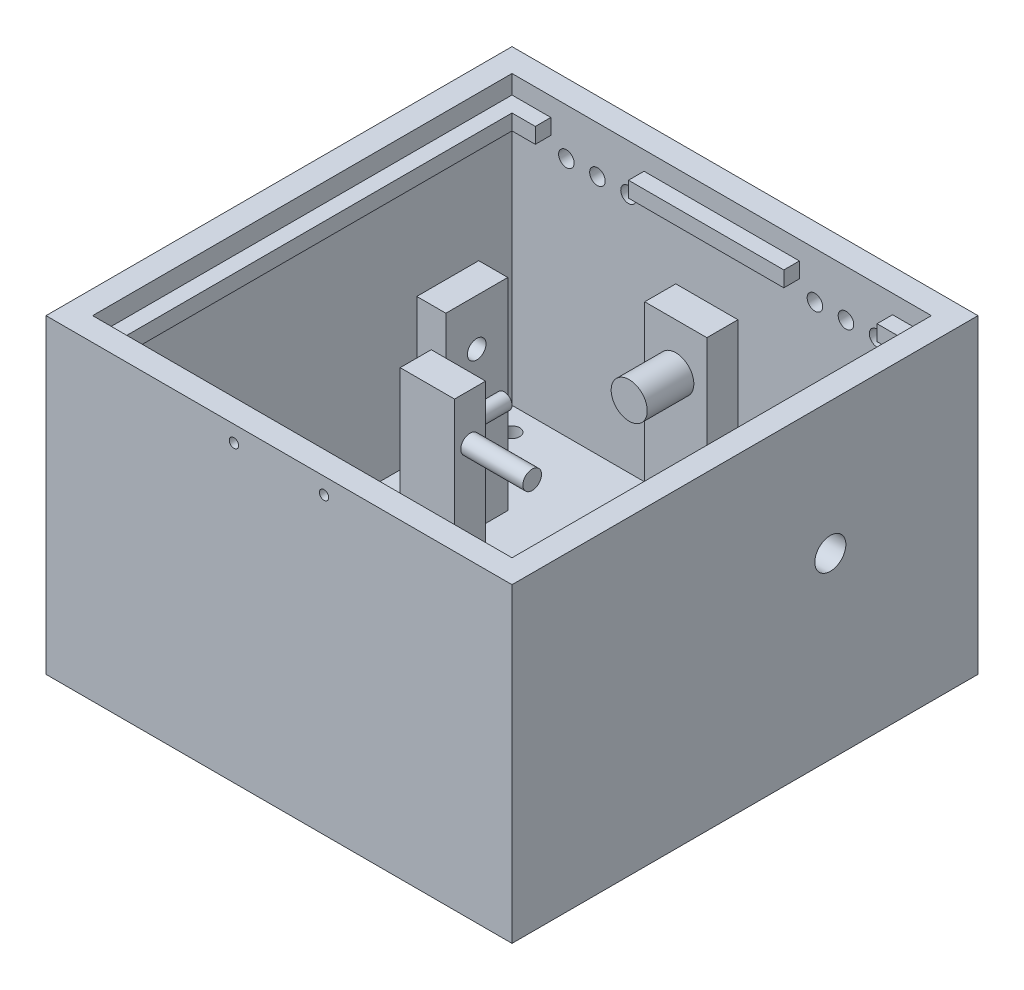
SolidWorks part; units mm, degrees
material "Cedar"
ref_plane "Front" through (0, 0, 0) normal (0, 0, 1) x (1, 0, 0)
ref_plane "Top" through (0, 0, 0) normal (0, 1, 0) x (1, 0, 0)
ref_plane "Right" through (0, 0, 0) normal (1, 0, 0) x (0, 0, -1)
sketch "Sketch1" plane through (0, 0, 0) normal (0, 1, 0) x (1, 0, 0)
  line L1 (-75, -75) -> (75, -75)
  line L2 (-75, -75) -> (-75, 75)
  line L3 (-75, 75) -> (75, 75)
  line L4 (75, -75) -> (75, 75)
  line L5 (-75, -75) -> (75, 75) construction
  line L6 (-75, 75) -> (75, -75) construction
  point P0 (0, 0)
  dimension "D1" = 150
  dimension "D2" = 150
extrude "Boss-Extrude1" add sketch "Sketch1" along normal blind 7.5
sketch "Sketch2" plane through (0, 7.5, 0) normal (0, 1, 0) x (1, 0, 0)
  line L1 (-67.5, -67.5) -> (67.5, -67.5)
  line L2 (-67.5, -67.5) -> (-67.5, 67.5)
  line L3 (-67.5, 67.5) -> (67.5, 67.5)
  line L4 (67.5, -67.5) -> (67.5, 67.5)
  line L5 (-67.5, -67.5) -> (67.5, 67.5) construction
  line L6 (-67.5, 67.5) -> (67.5, -67.5) construction
  line L7 (-75, -75) -> (75, -75)
  line L8 (-75, -75) -> (-75, 75)
  line L9 (-75, 75) -> (75, 75)
  line L10 (75, -75) -> (75, 75)
  line L11 (-75, -75) -> (75, 75) construction
  line L12 (-75, 75) -> (75, -75) construction
  point P0 (0, 0)
  point P5 (0, 0)
  dimension "D1" = 135
  dimension "D2" = 135
extrude "Boss-Extrude2" add sketch "Sketch2" along normal blind 92.5
sketch "Sketch3" plane through (0, 7.5, 0) normal (0, 1, 0) x (1, 0, 0)
  line L0 (0, -4.125) -> (0, 4.125) construction
  line L1 (-10, 62.7245) -> (10, 62.7245)
  line L2 (-10, 62.7245) -> (-10, 52.7245)
  line L3 (-10, 52.7245) -> (10, 52.7245)
  line L4 (10, 62.7245) -> (10, 52.7245)
  line L5 (-10, 62.7245) -> (10, 52.7245) construction
  line L6 (-10, 52.7245) -> (10, 62.7245) construction
  point P0 (0, 57.7245)
  dimension "D1" = 10
  dimension "D2" = 20
extrude "Boss-Extrude3" add sketch "Sketch3" along normal blind 65
sketch "Sketch4" plane through (0, 0, -52.7245) normal (0, 0, 1) x (1, 0, 0)
  line L0 (0, -4.125) -> (0, 4.125) construction
  line L2 (-10, 7.5) -> (10, 7.5) construction
  circle A0 centre (0, 57.5) radius 5.8075
  dimension "D1" = 11.615
  dimension "D2" = 50
extrude "Boss-Extrude4" add sketch "Sketch4" along normal blind 15 contours A0
sketch "Sketch5" plane through (0, 7.5, 0) normal (0, 1, 0) x (1, 0, 0)
  line L0 (-67.5, -67.5) -> (67.5, -67.5) construction
  line L1 (-48.1782, 37.4665) -> (-38.8218, 37.4665)
  line L2 (-48.1782, 37.4665) -> (-48.1782, 17.5335)
  line L3 (-48.1782, 17.5335) -> (-38.8218, 17.5335)
  line L4 (-38.8218, 37.4665) -> (-38.8218, 17.5335)
  line L5 (-48.1782, 37.4665) -> (-38.8218, 17.5335) construction
  line L6 (-48.1782, 17.5335) -> (-38.8218, 37.4665) construction
  line L7 (-67.5, 67.5) -> (-67.5, -67.5) construction
  point P0 (-43.5, 27.5)
  dimension "D1" = 95
  dimension "D2" = 9.3563
  dimension "D3" = 19.933
  dimension "D4" = 24
extrude "Boss-Extrude5" add sketch "Sketch5" along normal blind 65
sketch "Sketch6" plane through (-38.8218, 0, 0) normal (1, 0, 0) x (0, 0, -1)
  line L1 (17.5335, 7.5) -> (37.4665, 7.5) construction
  line L2 (37.4665, 72.5) -> (37.4665, 7.5) construction
  circle A0 centre (27.4665, 57.5) radius 3
  dimension "D1" = 6
  dimension "D2" = 50
  dimension "D3" = 10
sketch "Sketch7" plane through (0, 7.5, 0) normal (0, 1, 0) x (1, 0, 0)
  line L0 (-67.5, -67.5) -> (67.5, -67.5) construction
  line L1 (-23.5, 0) -> (-13.5, 0)
  line L2 (-23.5, 0) -> (-23.5, -5)
  line L3 (-23.5, -5) -> (-13.5, -5)
  line L4 (-13.5, 0) -> (-13.5, -5)
  line L5 (-23.5, 0) -> (-13.5, -5) construction
  line L6 (-23.5, -5) -> (-13.5, 0) construction
  line L7 (-67.5, 67.5) -> (-67.5, -67.5) construction
  line L9 (-23.5, 0) -> (-31, 0)
  line L10 (-23.5, 0) -> (-23.5, -5)
  line L11 (-23.5, -5) -> (-31, -5)
  line L12 (-31, 0) -> (-31, -5)
  point P0 (-18.5, -2.5)
  dimension "D1" = 5
  dimension "D2" = 10
  dimension "D3" = 65
  dimension "D4" = 49
  dimension "D5" = 7.5
  dimension "D6" = 5
extrude "Boss-Extrude7" add sketch "Sketch7" along normal blind 65 contours L9 L12 L11 L2 | L4 L1 L2 L3
sketch "Sketch8" plane through (0, 0, 0) normal (0, 0, -1) x (-1, 0, 0)
  line L0 (13.5, 7.5) -> (31, 7.5) construction
  line L1 (13.5, 72.5) -> (13.5, 7.5) construction
  circle A0 centre (20, 57.5) radius 2.5
  dimension "D1" = 5
  dimension "D2" = 50
  dimension "D3" = 6.5
extrude "Boss-Extrude8" add sketch "Sketch8" along normal blind 17.5
sketch "Sketch9" plane through (-13.5, 0, 0) normal (1, 0, 0) x (0, 0, -1)
  line L0 (-5, 72.5) -> (-5, 7.5) construction
  line L1 (-5, 7.5) -> (0, 7.5) construction
  circle A0 centre (10, 57.5) radius 3
  dimension "D1" = 6
  dimension "D2" = 15
  dimension "D3" = 50
sketch "Sketch10" plane through (0, 7.5, 0) normal (0, 1, 0) x (1, 0, 0)
  line L1 (-31, 0) -> (-13.5, 0)
  line L2 (-31, 0) -> (-31, 5)
  line L3 (-31, 5) -> (-13.5, 5)
  line L4 (-13.5, 0) -> (-13.5, 5)
  dimension "D1" = 17.5
  dimension "D2" = 5
extrude "Boss-Extrude10" add sketch "Sketch10" along normal blind 65
sketch "Sketch12" plane through (-13.5, 0, 0) normal (1, 0, 0) x (0, 0, -1)
  line L2 (5, 7.5) -> (-5, 7.5) construction
  line L3 (75, 100) -> (75, 0) construction
  circle A0 centre (0, 57.5) radius 3
  dimension "D1" = 6
  dimension "D2" = 75
  dimension "D3" = 50
extrude "Boss-Extrude11" add sketch "Sketch12" along normal blind 20
extrude "Cut-Extrude1" cut sketch "Sketch6" against normal blind 10
sketch "Sketch13" plane through (0, 7.5, 0) normal (0, 1, 0) x (1, 0, 0)
  line L0 (67.5, 67.5) -> (-67.5, 67.5) construction
  line L1 (18.2, 21.5) -> (34.2, 21.5)
  line L2 (18.2, 21.5) -> (18.2, 33.5)
  line L3 (18.2, 33.5) -> (34.2, 33.5)
  line L4 (34.2, 21.5) -> (34.2, 33.5)
  line L5 (18.2, 21.5) -> (34.2, 33.5) construction
  line L6 (18.2, 33.5) -> (34.2, 21.5) construction
  line L7 (67.5, -67.5) -> (67.5, 67.5) construction
  point P0 (26.2, 27.5)
  dimension "D1" = 34
  dimension "D2" = 33.3
  dimension "D3" = 12
  dimension "D4" = 16
extrude "Boss-Extrude12" add sketch "Sketch13" along normal blind 12.5
sketch "Sketch14" plane through (0, 7.5, 0) normal (0, 1, 0) x (1, 0, 0)
  line L0 (-67.5, -67.5) -> (67.5, -67.5) construction
  line L1 (30, -7.5) -> (65, -7.5)
  line L2 (30, -7.5) -> (30, 33.5)
  line L3 (30, 33.5) -> (65, 33.5)
  line L4 (65, -7.5) -> (65, 33.5)
  line L5 (30, -7.5) -> (65, 33.5) construction
  line L6 (30, 33.5) -> (65, -7.5) construction
  point P0 (47.5, 13)
  dimension "D1" = 35
  dimension "D2" = 41
  dimension "D3" = 20
  dimension "D4" = 60
extrude "Boss-Extrude13" add sketch "Sketch14" along normal blind 31
sketch "Sketch15" plane through (75, 0, 0) normal (1, 0, 0) x (0, 0, -1)
  line L0 (75, 100) -> (75, 0) construction
  line L1 (-75, 0) -> (75, 0) construction
  circle A0 centre (27.4665, 57.5) radius 5
  dimension "D1" = 10
  dimension "D2" = 47.5335
  dimension "D3" = 57.5
extrude "Cut-Extrude2" cut sketch "Sketch15" against normal blind 10
sketch "Sketch16" plane through (0, 0, 67.5) normal (0, 0, -1) x (-1, 0, 0)
  line L0 (-75, 100) -> (-75, 0) construction
  line L1 (-75, 94) -> (75, 94)
  line L2 (-75, 94) -> (-75, 89)
  line L3 (-75, 89) -> (75, 89)
  line L4 (75, 94) -> (75, 89)
  dimension "D1" = 150
  dimension "D2" = 0
  dimension "D3" = 5
  dimension "D4" = 6
extrude "Boss-Extrude14" add sketch "Sketch16" along normal blind 5
sketch "Sketch17" plane through (0, 0, -67.5) normal (0, 0, 1) x (1, 0, 0)
  line L0 (-75, 100) -> (-75, 0) construction
  line L1 (-75, 94) -> (75, 94)
  line L2 (-75, 94) -> (-75, 89)
  line L3 (-75, 89) -> (75, 89)
  line L4 (75, 94) -> (75, 89)
  line L5 (75, 100) -> (75, 0) construction
  line L6 (-75, 100) -> (75, 100) construction
  line L8 (-55, 94) -> (-25, 94)
  line L9 (-55, 94) -> (-55, 89)
  line L10 (-55, 89) -> (-25, 89)
  line L11 (-25, 94) -> (-25, 89)
  line L12 (25, 94) -> (55, 94)
  line L13 (25, 94) -> (25, 89)
  line L14 (25, 89) -> (55, 89)
  line L15 (55, 94) -> (55, 89)
  line M4 (67.5, 7.5) -> (67.5, 100)
  line M6 (-67.5, 100) -> (-67.5, 7.5)
  dimension "D1" = 5
  dimension "D2" = 6
  dimension "D3" = 20
  dimension "D4" = 20
  dimension "D5" = 30
  dimension "D6" = 30
extrude "Boss-Extrude15" add sketch "Sketch17" along normal blind 5 contours L9 L1 L3 M6 | L13 L1 L11 L3 | L1 L15 L3 M4
sketch "Sketch18" plane through (67.5, 0, 0) normal (-1, 0, 0) x (0, 0, 1)
  line L0 (-75, 100) -> (-75, 0) construction
  line L1 (-75, 94) -> (75, 94)
  line L2 (-75, 94) -> (-75, 89)
  line L3 (-75, 89) -> (75, 89)
  line L4 (75, 94) -> (75, 89)
  line L5 (75, 100) -> (75, 0) construction
  line L6 (-75, 100) -> (75, 100) construction
  dimension "D1" = 5
  dimension "D2" = 6
extrude "Boss-Extrude16" add sketch "Sketch18" along normal blind 5
sketch "Sketch19" plane through (-67.5, 0, 0) normal (1, 0, 0) x (0, 0, -1)
  line L0 (-75, 100) -> (-75, 0) construction
  line L1 (-75, 94) -> (75, 94)
  line L2 (-75, 94) -> (-75, 89)
  line L3 (-75, 89) -> (75, 89)
  line L4 (75, 94) -> (75, 89)
  line L5 (75, 100) -> (75, 0) construction
  line L6 (-75, 100) -> (75, 100) construction
  dimension "D1" = 5
  dimension "D2" = 6
extrude "Boss-Extrude17" add sketch "Sketch19" along normal blind 5
sketch "Sketch20" plane through (0, 0, -75) normal (0, 0, -1) x (-1, 0, 0)
  line L2 (-75, 100) -> (-75, 0) construction
  line L3 (-75, 100) -> (75, 100) construction
  line L4 (75, 100) -> (75, 0) construction
  circle A0 centre (-50, 85) radius 2.5
  circle A1 centre (-40, 85) radius 2.5
  circle A2 centre (-30, 85) radius 2.5
  circle A3 centre (30, 85) radius 2.5
  circle A4 centre (40, 85) radius 2.5
  circle A5 centre (50, 85) radius 2.5
  dimension "D1" = 5
  dimension "D2" = 5
  dimension "D3" = 5
  dimension "D4" = 5
  dimension "D5" = 5
  dimension "D6" = 5
  dimension "D7" = 10
  dimension "D8" = 10
  dimension "D9" = 10
  dimension "D10" = 10
  dimension "D11" = 25
  dimension "D12" = 25
  dimension "D13" = 15
  dimension "D14" = 15
  dimension "D15" = 15
  dimension "D16" = 15
  dimension "D17" = 15
  dimension "D18" = 15
extrude "Cut-Extrude3" cut sketch "Sketch20" against normal blind 10
sketch "Sketch21" plane through (0, 0, 0) normal (0, -1, 0) x (1, 0, 0)
  line L0 (-75, -75) -> (-75, 75) construction
  line L1 (75, -75) -> (-75, -75) construction
  line L2 (75, 75) -> (75, -75) construction
  line L3 (-75, 75) -> (75, 75) construction
  circle A0 centre (-60, 60) radius 2.5
  circle A1 centre (60, 60) radius 2.5
  circle A2 centre (-60, -60) radius 2.5
  circle A3 centre (60, -60) radius 2.5
  dimension "D1" = 5
  dimension "D2" = 5
  dimension "D3" = 5
  dimension "D4" = 5
  dimension "D5" = 15
  dimension "D6" = 15
  dimension "D7" = 15
  dimension "D8" = 15
  dimension "D9" = 15
  dimension "D10" = 15
  dimension "D11" = 15
  dimension "D12" = 15
extrude "Cut-Extrude4" cut sketch "Sketch21" against normal blind 10
sketch "Sketch22" plane through (0, 0, 75) normal (0, 0, 1) x (1, 0, 0)
  line L0 (-75, 100) -> (-75, 0) construction
  line L1 (-75, 100) -> (75, 100) construction
  circle A0 centre (-14.5, 94.75) radius 1.5
  circle A2 centre (14.5, 94.75) radius 1.5
  dimension "D1" = 3
  dimension "D2" = 3
  dimension "D3" = 5.25
  dimension "D4" = 60.5
  dimension "D5" = 29
  dimension "D6" = 5.25
extrude "Cut-Extrude5" cut sketch "Sketch22" against normal blind 5
sketch "Sketch23" plane through (0, 38.5, 0) normal (0, 1, 0) x (1, 0, 0)
  circle A0 centre (32.5, 8.61) radius 1
  circle A1 centre (32.5, 27.61) radius 1
  circle A2 centre (63, 31.61) radius 0.6
  circle A3 centre (57, 31.61) radius 0.6
  circle A4 centre (57, 7.31) radius 0.6
  circle A5 centre (63, 7.31) radius 0.6
  circle A6 centre (57, 28.9084) radius 0.6
  circle A7 centre (63, 28.91) radius 0.6
  circle A8 centre (63, 4.61) radius 0.6
  circle A9 centre (57, 4.61) radius 0.6
  dimension "D1" = 2
  dimension "D2" = 2
  dimension "D3" = 1.2
  dimension "D4" = 1.2
  dimension "D5" = 1.2
  dimension "D6" = 1.2
  dimension "D7" = 1.2
  dimension "D8" = 1.2
  dimension "D11" = 1.2
  dimension "D12" = 1.2
  dimension "D9" = 6
  dimension "D10" = 2.7016
  dimension "D13" = 2.7
  dimension "D14" = 6
extrude "Cut-Extrude6" cut sketch "Sketch23" against normal blind 4
sketch "Sketch24" plane through (0, 20, 0) normal (0, 1, 0) x (1, 0, 0)
  line L0 (18.2, 33.5) -> (18.2, 21.5) construction
  line L1 (18.2, 21.5) -> (30, 21.5) construction
  line L2 (30, 33.5) -> (18.2, 33.5) construction
  circle A0 centre (23.7, 24.4665) radius 0.75
  circle A1 centre (23.7, 30.5) radius 0.75
  circle A2 centre (19.7, 31.7165) radius 0.5
  circle A3 centre (19.7, 23.2) radius 0.5
  dimension "D1" = 1.5
  dimension "D2" = 1
  dimension "D5" = 1
  dimension "D6" = 1.5
  dimension "D3" = 1.5
  dimension "D4" = 1.7
  dimension "D7" = 5.5
  dimension "D8" = 3
extrude "Cut-Extrude7" cut sketch "Sketch24" against normal blind 4
